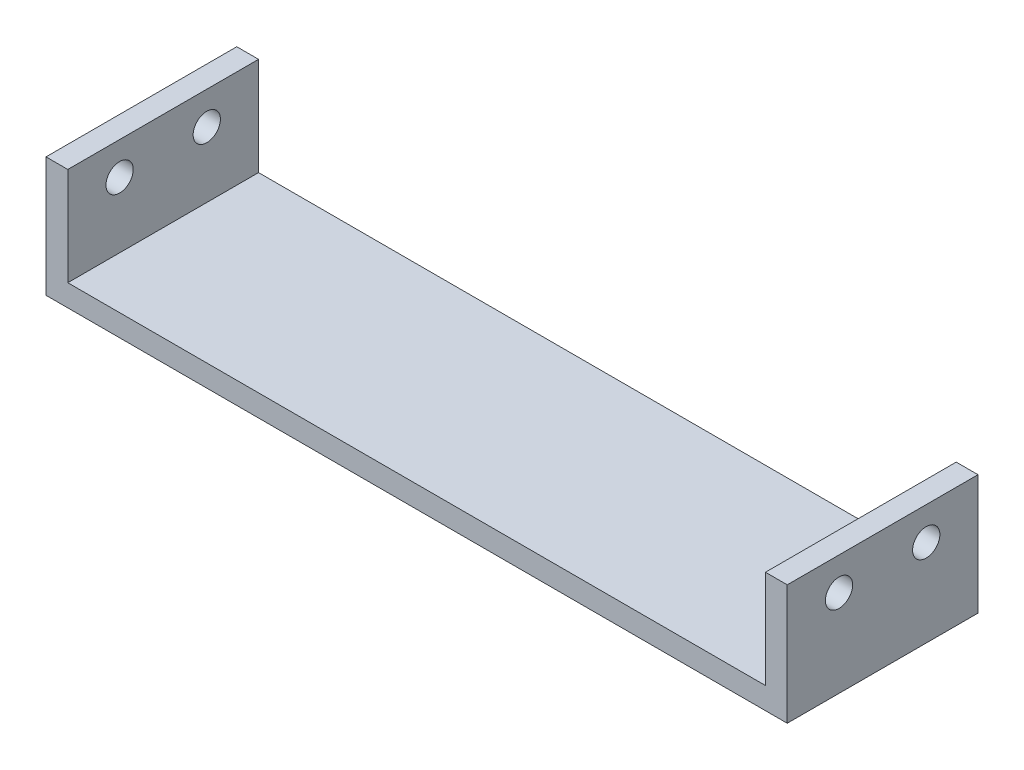
SolidWorks part; units mm, degrees
ref_plane "Front Plane" through (0, 0, 0) normal (0, 0, 1) x (1, 0, 0)
ref_plane "Top Plane" through (0, 0, 0) normal (0, 1, 0) x (1, 0, 0)
ref_plane "Right Plane" through (0, 0, 0) normal (1, 0, 0) x (0, 0, -1)
sketch "Sketch1" plane through (0, 0, 0) normal (1, 0, 0) x (0, 0, -1)
  line L1 (-56.7644, -1.96) -> (-39.2644, -1.96)
  line L2 (-56.7644, -1.96) -> (-56.7644, 9.04)
  line L3 (-56.7644, 9.04) -> (-39.2644, 9.04)
  line L4 (-39.2644, -1.96) -> (-39.2644, 9.04)
  dimension "D1" = 11
  dimension "D2" = 17.5
extrude "Boss-Extrude1" add sketch "Sketch1" along normal blind 2
sketch "Sketch2" plane through (2, 0, 0) normal (1, 0, 0) x (0, 0, -1)
  line L0 (-39.2644, -1.96) -> (-39.2644, 9.04) construction
  line L1 (-56.7644, -1.96) -> (-39.2644, -1.96)
  line L2 (-56.7644, -1.96) -> (-56.7644, 0.04)
  line L3 (-56.7644, 0.04) -> (-39.2644, 0.04)
  line L4 (-39.2644, -1.96) -> (-39.2644, 0.04)
  dimension "D1" = 2
extrude "Boss-Extrude2" add sketch "Sketch2" along normal blind 64
sketch "Sketch3" plane through (66, 0, 0) normal (1, 0, 0) x (0, 0, -1)
  line L0 (-39.2644, 9.04) -> (-56.7644, 9.04) construction
  line L1 (-56.7644, -1.96) -> (-39.2644, -1.96)
  line L2 (-56.7644, -1.96) -> (-56.7644, 9.04)
  line L3 (-56.7644, 9.04) -> (-39.2644, 9.04)
  line L4 (-39.2644, -1.96) -> (-39.2644, 9.04)
  line L5 (-39.2644, 0.04) -> (-39.2644, 9.04) construction
extrude "Boss-Extrude3" add sketch "Sketch3" along normal blind 2
sketch "Sketch4" plane through (68, 0, 0) normal (1, 0, 0) x (0, 0, -1)
  line L2 (-39.2644, 9.04) -> (-56.7644, 9.04) construction
  line L3 (-39.2644, 9.04) -> (-56.7644, 9.04) construction
  circle A0 centre (-52.0144, 6.04) radius 1.25
  circle A1 centre (-44.0144, 6.04) radius 1.25
  point P4 (-48.0144, 9.04)
  point P7 (-48.0144, 9.04)
  dimension "D1" = 4
  dimension "D4" = 3
  dimension "D2" = 4
  dimension "D3" = 3
extrude "Cut-Extrude1" cut sketch "Sketch4" against normal blind 68
